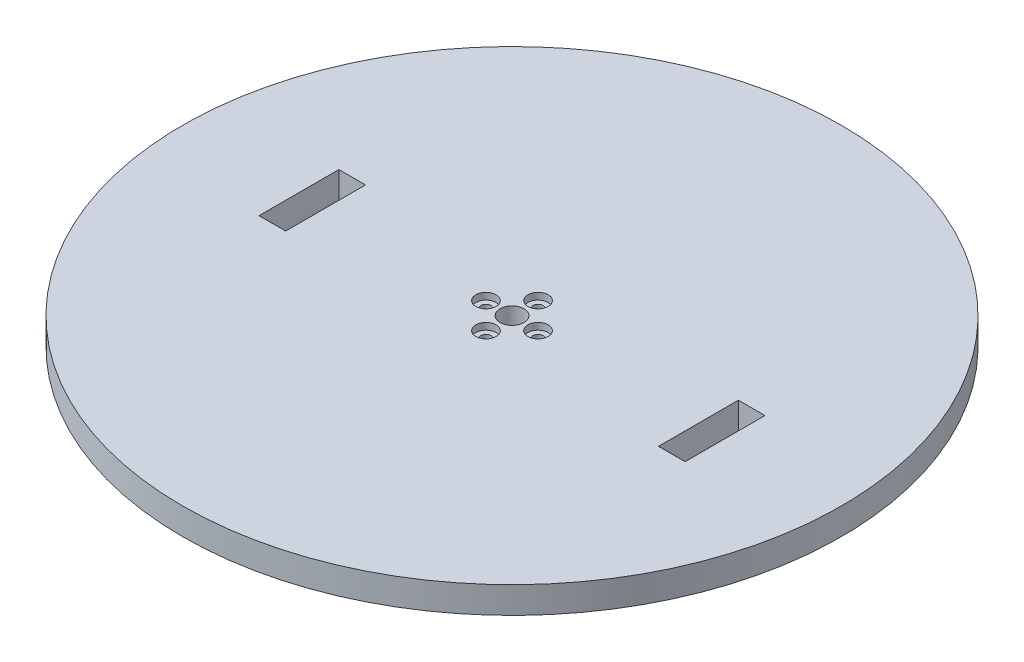
SolidWorks part; units mm, degrees
material "ABS"
ref_plane "Front Plane" through (0, 0, 0) normal (0, 0, 1) x (1, 0, 0)
ref_plane "Top Plane" through (0, 0, 0) normal (0, 1, 0) x (1, 0, 0)
ref_plane "Right Plane" through (0, 0, 0) normal (1, 0, 0) x (0, 0, -1)
sketch "Sketch1" plane through (0, 0, 0) normal (0, 1, 0) x (1, 0, 0)
  circle A0 centre (0, 0) radius 123.75
  dimension "D1" = 247.5
extrude "Boss-Extrude1" add sketch "Sketch1" along normal blind 10
sketch "Sketch2" plane through (0, 10, 0) normal (0, 1, 0) x (1, 0, 0)
  circle A0 centre (0, 0) radius 9.779
  circle A1 centre (0, 9.779) radius 1.905
  dimension "D1" = 19.558
  dimension "D2" = 3.81
extrude "Cut-Extrude2" cut sketch "Sketch2" against normal through all contours A0 A1 | A0 A1
pattern_circular "CirPattern1" count 4 every 90 about axis through (0, 0, 0) along (0, 1, 0) of "Cut-Extrude2"
sketch "Sketch3" plane through (0, 10, 0) normal (0, 1, 0) x (1, 0, 0)
  circle A0 centre (0, 0) radius 4.5
  dimension "D1" = 9
extrude "Cut-Extrude3" cut sketch "Sketch3" against normal through all
sketch "Sketch4" plane through (0, 10, 0) normal (0, 1, 0) x (1, 0, 0)
  circle A0 centre (0, 9.779) radius 3.81
  dimension "D1" = 7.62
extrude "Cut-Extrude4" cut sketch "Sketch4" against normal blind 2.54
pattern_circular "CirPattern2" count 4 every 90 about axis through (0, 0, 0) along (0, 1, 0) of "Cut-Extrude4"
sketch "Sketch5" plane through (0, 10, 0) normal (0, 1, 0) x (1, 0, 0)
  line L0 (0, -123.75) -> (0, 123.75) construction
  line L1 (123.75, 0) -> (-123.75, 0) construction
  line L2 (80, -15) -> (70, -15)
  line L3 (80, -15) -> (80, 15)
  line L4 (80, 15) -> (70, 15)
  line L5 (70, -15) -> (70, 15)
  line L6 (-80, 15) -> (-70, 15)
  line L7 (-70, -15) -> (-70, 15)
  line L8 (-80, -15) -> (-70, -15)
  line L9 (-80, -15) -> (-80, 15)
  circle A0 centre (0, 0) radius 123.75 construction
  dimension "D1" = 10
  dimension "D2" = 30
  dimension "D3" = 15
  dimension "D4" = 70
extrude "Cut-Extrude5" cut sketch "Sketch5" against normal through all
